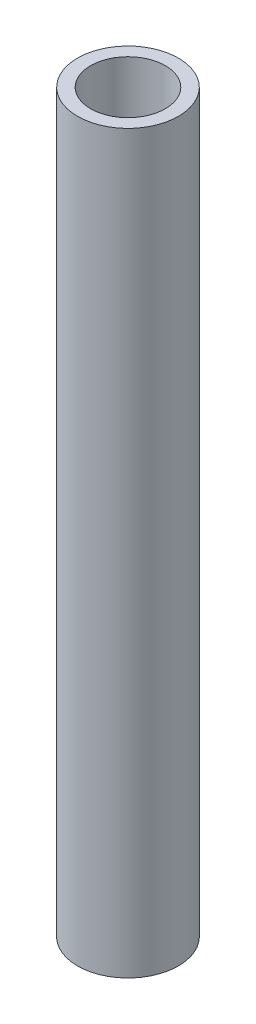
SolidWorks part; units mm, degrees
material "PVC Rigid"
ref_plane "Front" through (0, 0, 0) normal (0, 0, 1) x (1, 0, 0)
ref_plane "Top" through (0, 0, 0) normal (0, 1, 0) x (1, 0, 0)
ref_plane "Right" through (0, 0, 0) normal (1, 0, 0) x (0, 0, -1)
sketch "Sketch1" plane through (0, 0, 0) normal (0, 1, 0) x (1, 0, 0)
  circle A0 centre (0, 0) radius 7.8994
  circle A1 centre (0, 0) radius 10.668
  dimension "D1" = 15.7988
  dimension "D2" = 21.336
extrude "Boss-Extrude1" add sketch "Sketch1" along normal blind 155.575
